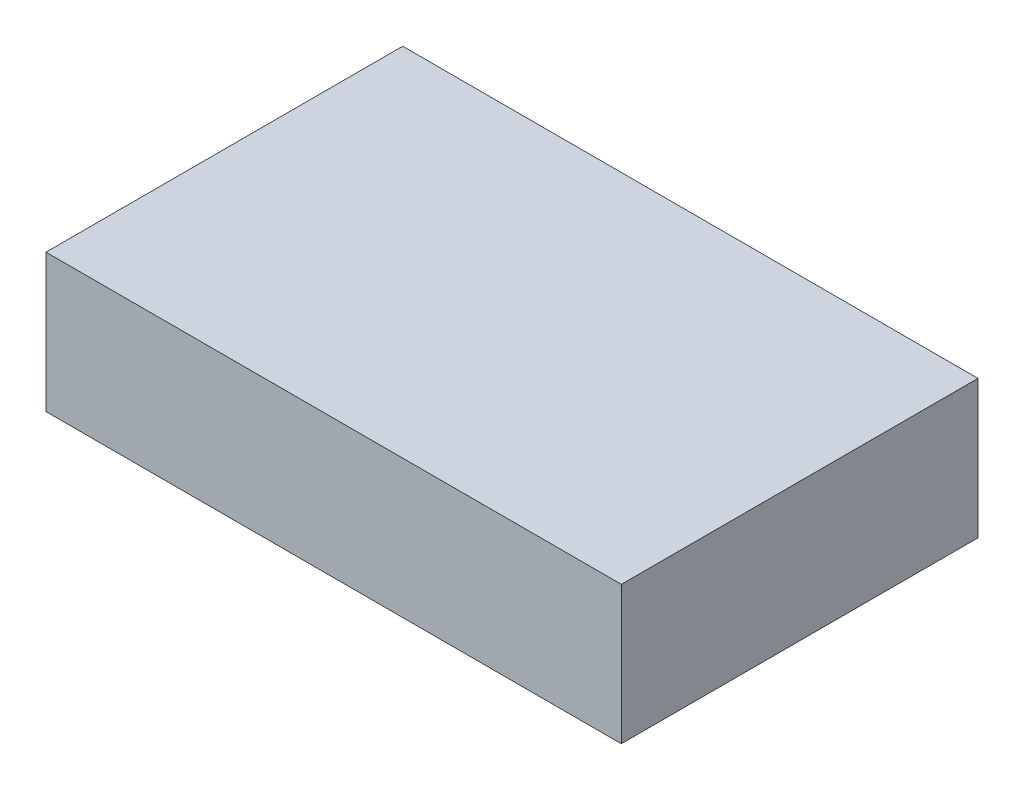
SolidWorks part; units mm, degrees
ref_plane "Front Plane" through (0, 0, 0) normal (0, 0, 1) x (1, 0, 0)
ref_plane "Top Plane" through (0, 0, 0) normal (0, 1, 0) x (1, 0, 0)
ref_plane "Right Plane" through (0, 0, 0) normal (1, 0, 0) x (0, 0, -1)
sketch "Sketch1" plane through (0, 0, 0) normal (0, 1, 0) x (1, 0, 0)
  line L1 (-79.375, -49.2125) -> (79.375, -49.2125)
  line L2 (-79.375, -49.2125) -> (-79.375, 49.2125)
  line L3 (-79.375, 49.2125) -> (79.375, 49.2125)
  line L4 (79.375, -49.2125) -> (79.375, 49.2125)
  line L5 (-79.375, -49.2125) -> (79.375, 49.2125) construction
  line L6 (-79.375, 49.2125) -> (79.375, -49.2125) construction
  point P0 (0, 0)
  dimension "D1" = 158.75
  dimension "D2" = 98.425
extrude "Boss-Extrude1" add sketch "Sketch1" along normal blind 38.1
